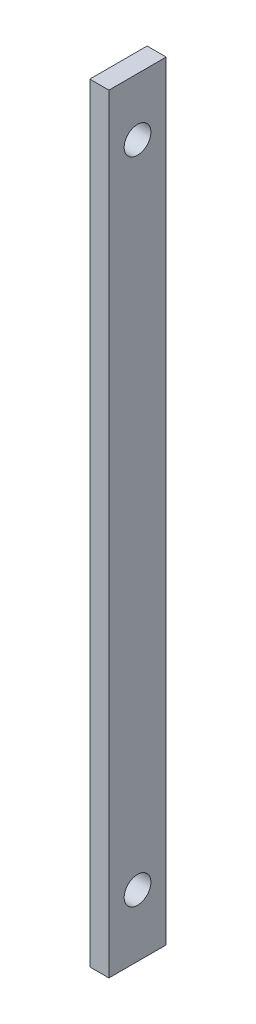
SolidWorks part; units mm, degrees
ref_plane "Front Plane" through (0, 0, 0) normal (0, 0, 1) x (1, 0, 0)
ref_plane "Top Plane" through (0, 0, 0) normal (0, 1, 0) x (1, 0, 0)
ref_plane "Right Plane" through (0, 0, 0) normal (1, 0, 0) x (0, 0, -1)
sketch "Sketch1" plane through (0, 0, 0) normal (1, 0, 0) x (0, 0, -1)
  line L1 (-43.8427, 47.535) -> (-28.8427, 47.535)
  line L2 (-43.8427, 47.535) -> (-43.8427, -153.7106)
  line L3 (-43.8427, -153.7106) -> (-28.8427, -153.7106)
  line L4 (-28.8427, 47.535) -> (-28.8427, -153.7106)
  dimension "D1" = 15
extrude "Boss-Extrude1" add sketch "Sketch1" along normal blind 5 contours L2 L3 L4 L1
sketch "Sketch2" plane through (5, 0, 0) normal (1, 0, 0) x (0, 0, -1)
  line L0 (-36.3427, 47.535) -> (-36.3427, -153.7106) construction
  line L1 (-43.8427, 47.535) -> (-28.8427, 47.535) construction
  line L2 (-43.8427, -153.7106) -> (-28.8427, -153.7106) construction
hole_wizard "Tap Drill for M8x1.0 Tap1" positions "Sketch5" profile "Sketch6" hole size "M8x1.0" standard "ANSI Metric" end condition through all
sketch "Sketch5" plane through (5, 0, 0) normal (1, 0, 0) x (0, 0, -1)
  line L4 (-36.3427, 47.535) -> (-36.3427, -153.7106) construction
  point P0 (-36.3427, 32.535)
  point P2 (-36.3427, -137.4706)
  point P5 (-36.3427, 32.535)
  point P19 (-46.8897, 44.9914)
  point P20 (-46.8897, -10.8904)
  point P24 (0, 0)
  point P25 (-36.3427, -21.6617)
  dimension "D1" = 15
  dimension "D2" = 16.24
sketch "Sketch6" plane through (5, 32.535, 36.3427) normal (0, 1, 0) x (0, 0, -1)
  line L0 (0, 0) -> (0, 5)
  line L1 (0, 5) -> (3.5, 5)
  line L2 (3.5, 5) -> (3.5, 0)
  line L5 (3.5, 0) -> (0, 0)
  line L11 (0, -6.35) -> (0, 107.95) construction
  dimension "Thru Hole Dia." = 7
  dimension "Thru Hole Depth" = 5
ref_plane "Plane1" through (5, -153.7106, 28.8427) normal (0, 0, -1) x (-1, 0, 0)
